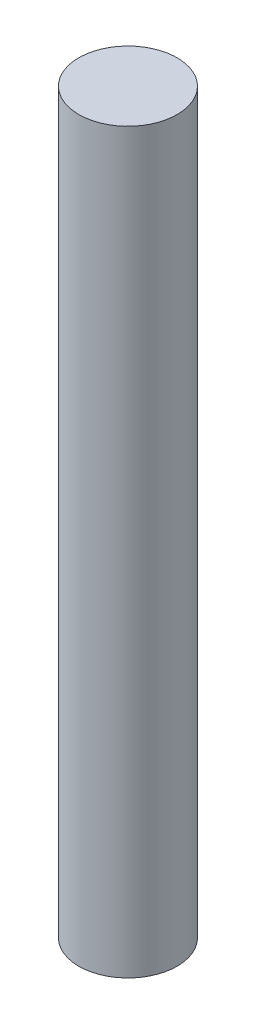
SolidWorks part; units mm, degrees
ref_plane "Front Plane" through (0, 0, 0) normal (0, 0, 1) x (1, 0, 0)
ref_plane "Top Plane" through (0, 0, 0) normal (0, 1, 0) x (1, 0, 0)
ref_plane "Right Plane" through (0, 0, 0) normal (1, 0, 0) x (0, 0, -1)
sketch "Sketch1" plane through (0, 0, 0) normal (0, 1, 0) x (1, 0, 0)
  circle A0 centre (0, 0) radius 10
extrude "Boss-Extrude1" add sketch "Sketch1" along normal blind 150
